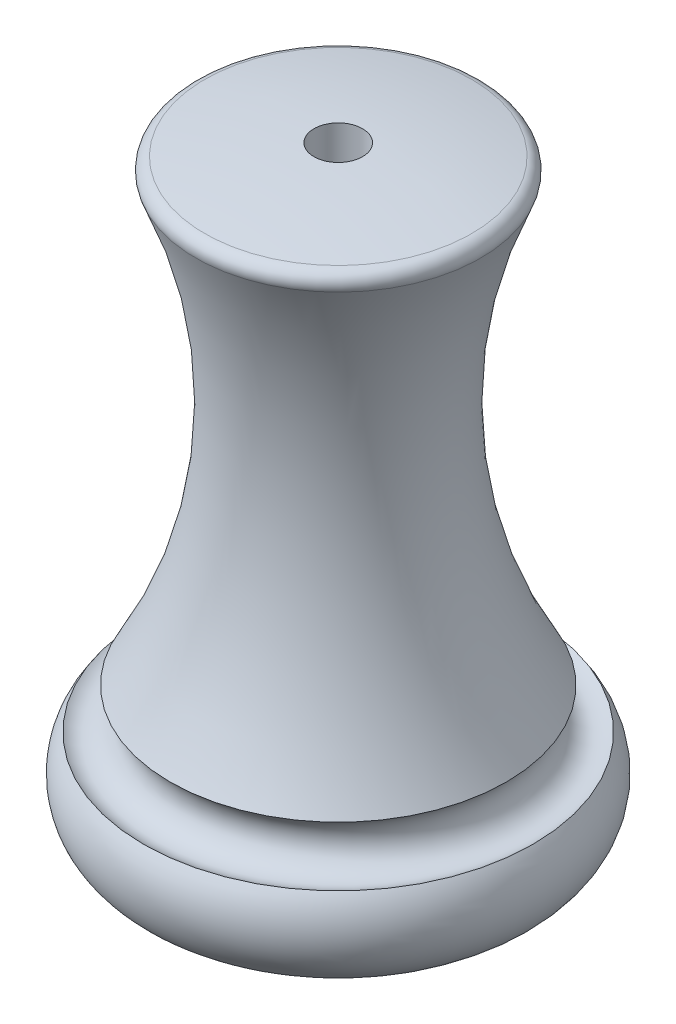
SolidWorks part; units mm, degrees
ref_plane "Front Plane" through (0, 0, 0) normal (0, 0, 1) x (1, 0, 0)
ref_plane "Top Plane" through (0, 0, 0) normal (0, 1, 0) x (1, 0, 0)
ref_plane "Right Plane" through (0, 0, 0) normal (1, 0, 0) x (0, 0, -1)
sketch "Sketch1" plane through (0, 0, 0) normal (1, 0, 0) x (0, 0, -1)
  line L0 (0, 0) -> (0, 50)
  line L1 (12, 0) -> (0, 0)
  arc A0 (0, 50) -> (11, 48.9831) centre (0, -10) cw
  arc A1 (11, 48.9831) -> (11.7323, 47.598) centre (10.8167, 48) cw
  arc A2 (11.7323, 47.598) -> (16.0397, 7.9463) centre (48.3574, 31.5168) ccw
  arc A3 (16.0397, 7.9463) -> (12, 0) centre (12, 5) cw
  point P11 (0, 0)
  point P12 (0, 0)
  point P13 (0, 0)
  point P14 (0, 0)
  dimension "D1" = 5
  dimension "D4" = 40
  dimension "D6" = 60
  dimension "D7" = 1
  dimension "D2" = 50
  dimension "D3" = 12
  dimension "D5" = 2
revolve "Revolve1" add sketch "Sketch1" angle 360 about L0
sketch "Sketch2" plane through (0, 0, 0) normal (1, 0, 0) x (0, 0, -1)
  circle A0 centre (14.9019, 9.5912) radius 2
  arc A1 (11.7323, 47.598) -> (16.0397, 7.9463) centre (48.3574, 31.5168) ccw construction
  point P3 (0, 0)
  point P4 (16.8443, 15.1681)
  point P5 (0, 0)
  point P9 (14.8598, 9.6556)
  dimension "D1" = 4
revolve "Cut-Revolve1" cut sketch "Sketch2" angle 360 about L0
sketch "Sketch3" plane through (0, 0, 0) normal (0, -1, 0) x (1, 0, 0)
  circle A0 centre (0, 0) radius 2
  dimension "D1" = 4
extrude "Cut-Extrude1" cut sketch "Sketch3" against normal through all
ref_plane "Plane1" through (0, 50, 0) normal (0, 1, 0) x (1, 0, 0)
